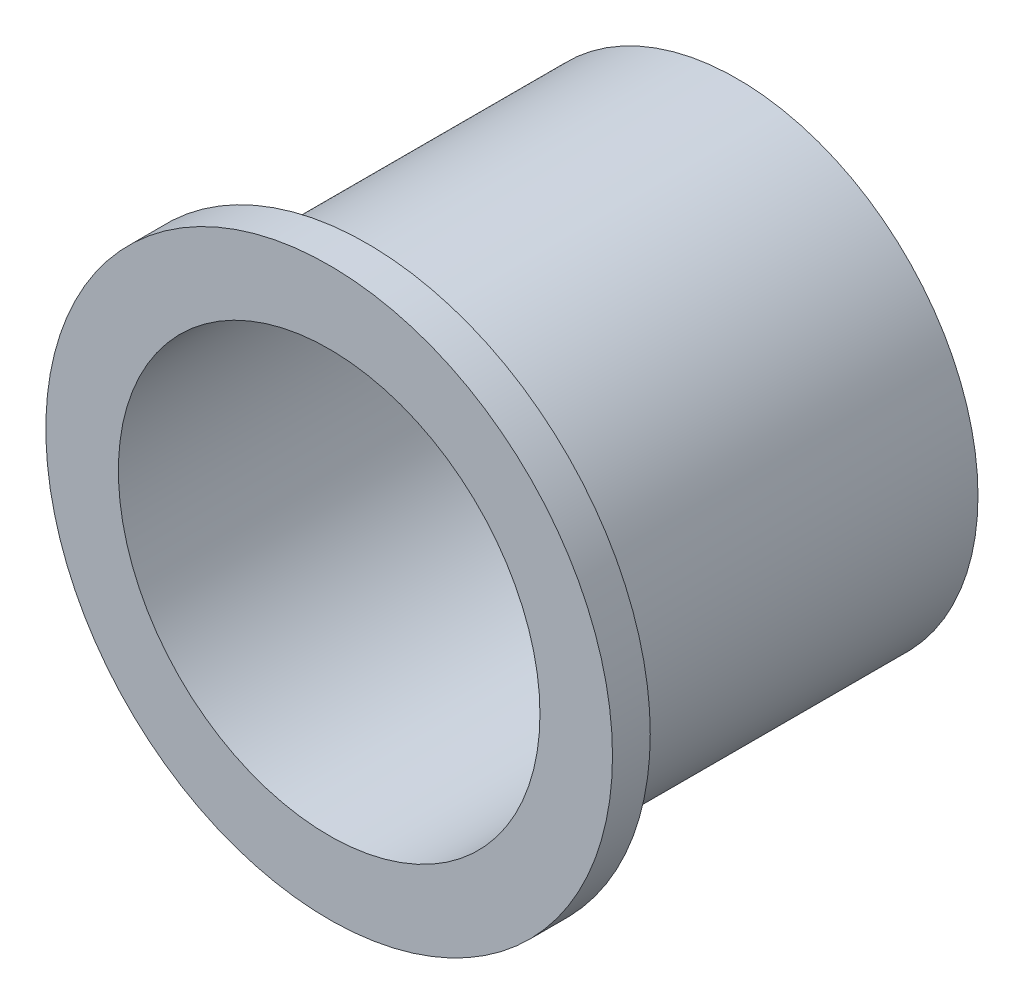
SolidWorks part; units mm, degrees
other "Internal" parameters "D1"=97.8064, "D2"=84.956, "D3"=164.5453, "D4"=190.5, "D5"=20.193
material "PE High Density"
ref_plane "Front Plane" through (0, 0, 0) normal (0, 0, 1) x (1, 0, 0)
ref_plane "Top Plane" through (0, 0, 0) normal (0, 1, 0) x (1, 0, 0)
ref_plane "Right Plane" through (0, 0, 0) normal (1, 0, 0) x (0, 0, -1)
other "Center of Mass"
sketch "Revolve Sketch" plane through (0, 0, 0) normal (1, 0, 0) x (0, 0, -1)
  line L0 (0, 190.5) -> (0, 141.732)
  line L1 (0, 141.732) -> (274.32, 141.732)
  line L2 (274.32, 141.732) -> (274.32, 161.925)
  line L3 (274.32, 161.925) -> (25.4, 161.925)
  line L4 (25.4, 161.925) -> (25.4, 190.5)
  line L5 (25.4, 190.5) -> (0, 190.5)
  line L6 (0, 0) -> (97.8064, 0) construction
  dimension "D1" = 141.732
  dimension "D2" = 161.925
  dimension "D3" = 190.5
  dimension "D4" = 25.4
  dimension "D5" = 274.32
revolve "Revolve Body" add sketch "Revolve Sketch" angle 360 about L6
ref_plane "Plane1" [suppressed] through (0, 0, -274.32) normal (0, 0, -1) x (-1, 0, 0)
ref_plane "Plane2" [suppressed] through (0, 0, 0) normal (0, 0, 1) x (1, 0, 0)
other "Intersect1" [suppressed]
equation "\"ID\"= 11.160in'for 12 NOM (EPG)"
equation "\"OD\"= 12.75in'for 12 NOM (EPG)"
equation "\"A\"= 10.8in'refer to EPG datasheet"
equation "\"T\"= 1in'refer to EPG datasheet"
equation "\"C\"= 15in'refer to EPG datasheet"
equation "\"D1@Revolve Sketch\" = \"ID\" / 2"
equation "\"D2@Revolve Sketch\" = \"OD\" / 2"
equation "\"D3@Revolve Sketch\" = \"C\" / 2"
equation "\"D4@Revolve Sketch\" = \"T\""
equation "\"D5@Revolve Sketch\" = \"A\""
